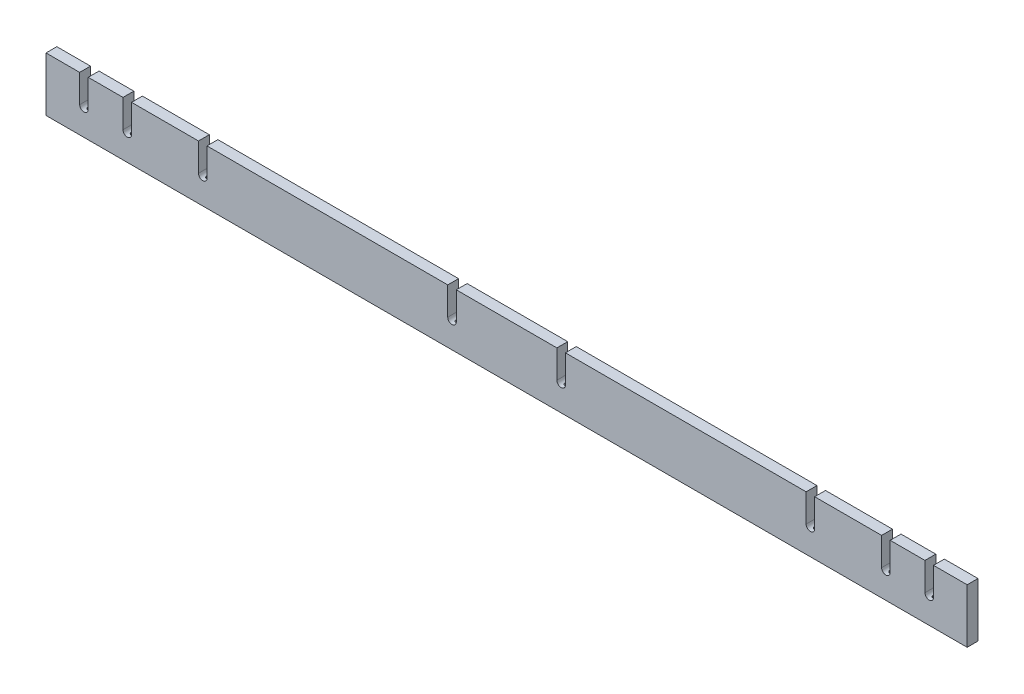
SolidWorks part; units mm, degrees
ref_plane "Front Plane" through (0, 0, 0) normal (0, 0, 1) x (1, 0, 0)
ref_plane "Top Plane" through (0, 0, 0) normal (0, 1, 0) x (1, 0, 0)
ref_plane "Right Plane" through (0, 0, 0) normal (1, 0, 0) x (0, 0, -1)
sketch "Sketch1" plane through (0, 0, 0) normal (0, 0, 1) x (1, 0, 0)
  line L0 (0, 0) -> (0, 1089.0775) construction
  line L3 (-539.75, 1028.7) -> (539.75, 1028.7)
  line L4 (-539.75, 1028.7) -> (-539.75, 965.2)
  line L5 (-539.75, 965.2) -> (539.75, 965.2)
  line L6 (0, 1028.7) -> (0, 965.2) construction
  line L7 (584.2, 0) -> (-584.2, 0) construction
  line L8 (539.75, 1028.7) -> (539.75, 965.2)
  dimension "D1" = 1028.7
  dimension "D2" = 63.5
  dimension "D3" = 1079.5
extrude "Extrude1" add sketch "Sketch1" along normal blind 12.7
sketch "Sketch4" plane through (0, 0, 0) normal (0, 0, -1) x (-1, 0, 0)
  line L0 (-68.95, 1028.7) -> (-68.95, 995.9)
  line L1 (-351.05, 1028.7) -> (-361.05, 1028.7)
  line L2 (-361.05, 1028.7) -> (-361.05, 995.9)
  line L3 (-361.05, 995.9) -> (-351.05, 995.9) construction
  line L4 (-351.05, 1028.7) -> (-351.05, 995.9)
  line L5 (-58.95, 1028.7) -> (-58.95, 995.9)
  line L6 (58.95, 1028.7) -> (58.95, 995.9)
  line L7 (68.95, 1028.7) -> (68.95, 995.9)
  line L8 (351.05, 1028.7) -> (351.05, 995.9)
  line L9 (361.05, 1028.7) -> (361.05, 995.9)
  line L10 (361.05, 1028.7) -> (351.05, 1028.7)
  line L12 (68.95, 1028.7) -> (58.95, 1028.7)
  line L13 (-58.95, 1028.7) -> (-68.95, 1028.7)
  line L14 (-539.75, 1028.7) -> (539.75, 1028.7) construction
  circle A0 centre (-356.05, 1000.9) radius 5 construction
  circle A1 centre (-63.95, 1000.9) radius 5 construction
  arc A2 (-351.05, 995.9) -> (-361.05, 995.9) centre (-356.05, 995.9) cw
  circle A3 centre (63.95, 1000.9) radius 5 construction
  circle A4 centre (356.05, 1000.9) radius 5 construction
  arc A6 (-58.95, 995.9) -> (-68.95, 995.9) centre (-63.95, 995.9) cw
  arc A8 (68.95, 995.9) -> (58.95, 995.9) centre (63.95, 995.9) cw
  arc A10 (361.05, 995.9) -> (351.05, 995.9) centre (356.05, 995.9) cw
  dimension "D1" = 10
extrude "Cut-Extrude1" cut sketch "Sketch4" against normal through all
sketch "Sketch6" plane through (0, 965.2, 0) normal (0, -1, 0) x (1, 0, 0)
  line L0 (-351.05, 12.7) -> (-361.05, 0) construction
  line L1 (-58.95, 0) -> (-68.95, 12.7) construction
  line L2 (68.95, 0) -> (58.95, 12.7) construction
  line L3 (361.05, 0) -> (351.05, 12.7) construction
  circle A0 centre (-356.05, 6.35) radius 2.0828
  circle A1 centre (356.05, 6.35) radius 2.0828
  circle A2 centre (63.95, 6.35) radius 2.0828
  circle A3 centre (-63.95, 6.35) radius 2.0828
  dimension "D1" = 4.1656
extrude "Cut-Extrude3" cut sketch "Sketch6" against normal through all
sketch "Sketch7" plane through (0, 0, 12.7) normal (0, 0, 1) x (1, 0, 0)
  line L0 (-361.05, 1028.7) -> (-539.75, 1028.7) construction
  line L2 (-361.05, 995.9) -> (-361.05, 1009.65) construction
  line L3 (-351.05, 995.9) -> (-351.05, 1009.65) construction
  line L4 (-449.5, 995.9) -> (-449.5, 1028.7)
  line L5 (-439.5, 1028.7) -> (-439.5, 995.9)
  line L6 (-500.3, 995.9) -> (-500.3, 1028.7)
  line L7 (-490.3, 1028.7) -> (-490.3, 995.9)
  line L9 (0, 965.2) -> (0, 1092.8513) construction
  line L10 (-539.75, 965.2) -> (539.75, 965.2) construction
  line L11 (490.3, 1028.7) -> (490.3, 995.9)
  line L12 (500.3, 995.9) -> (500.3, 1028.7)
  line L13 (439.5, 1028.7) -> (439.5, 995.9)
  line L14 (449.5, 995.9) -> (449.5, 1028.7)
  line L15 (-500.3, 1028.7) -> (-490.3, 1028.7)
  line L16 (-449.5, 1028.7) -> (-439.5, 1028.7)
  line L17 (439.5, 1028.7) -> (449.5, 1028.7)
  line L18 (490.3, 1028.7) -> (500.3, 1028.7)
  arc A0 (-361.05, 995.9) -> (-351.05, 995.9) centre (-356.05, 995.9) ccw construction
  arc A1 (-361.05, 995.9) -> (-351.05, 995.9) centre (-356.05, 995.9) ccw construction
  arc A2 (-449.5, 995.9) -> (-439.5, 995.9) centre (-444.5, 995.9) ccw
  arc A3 (-500.3, 995.9) -> (-490.3, 995.9) centre (-495.3, 995.9) ccw
  arc A4 (500.3, 995.9) -> (490.3, 995.9) centre (495.3, 995.9) cw
  arc A5 (449.5, 995.9) -> (439.5, 995.9) centre (444.5, 995.9) cw
  dimension "D1" = 444.5
  dimension "D2" = 495.3
extrude "Cut-Extrude4" cut sketch "Sketch7" against normal through all
sketch "Sketch8" plane through (0, 965.2, 0) normal (0, -1, 0) x (1, 0, 0)
  line L0 (-490.3, 0) -> (-500.3, 12.7) construction
  line L1 (-449.5, 12.7) -> (-439.5, 0) construction
  line L2 (0, 0) -> (0, 133.0225) construction
  circle A0 centre (-495.3, 6.35) radius 2.0828
  circle A1 centre (-444.5, 6.35) radius 2.0828
  circle A2 centre (-356.05, 6.35) radius 2.0828 construction
  circle A3 centre (444.5, 6.35) radius 2.0828
  circle A4 centre (495.3, 6.35) radius 2.0828
extrude "Cut-Extrude5" cut sketch "Sketch8" against normal through all
